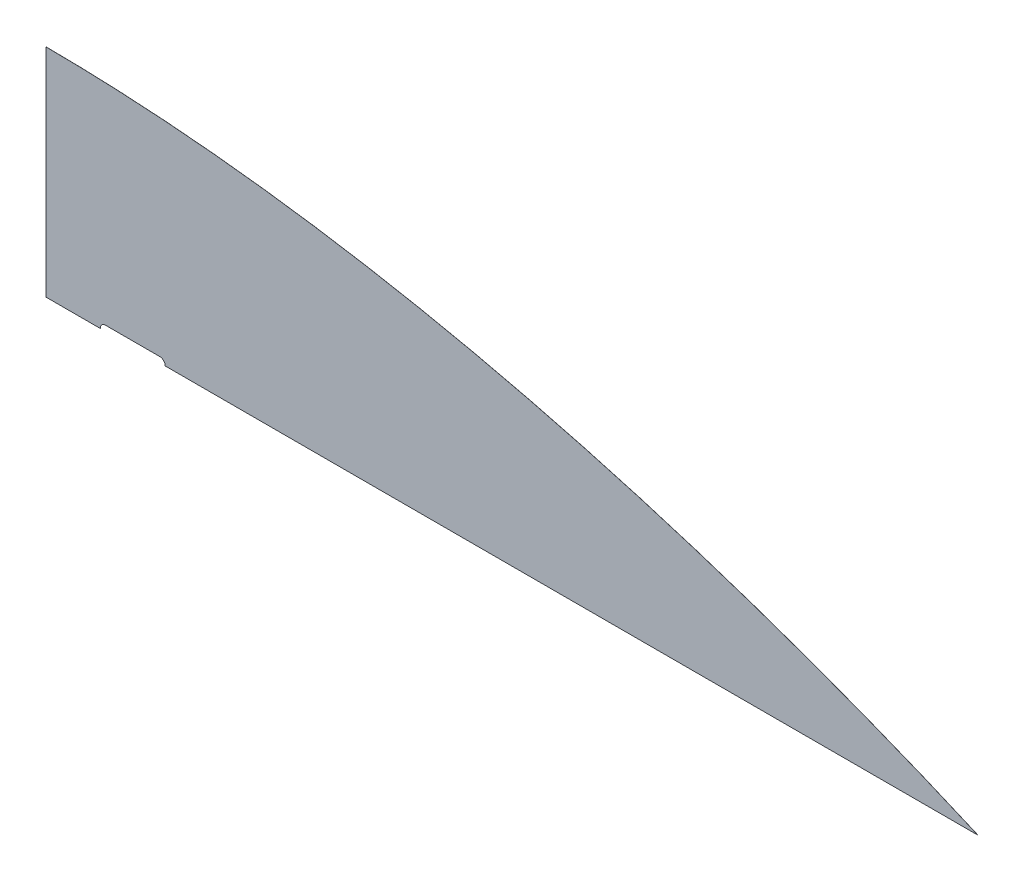
SolidWorks part; units mm, degrees
material "PC High Viscosity"
ref_plane "Front Plane" through (0, 0, 0) normal (0, 0, 1) x (1, 0, 0)
ref_plane "Top Plane" through (0, 0, 0) normal (0, 1, 0) x (1, 0, 0)
ref_plane "Right Plane" through (0, 0, 0) normal (1, 0, 0) x (0, 0, -1)
sketch "Sketch1" plane through (0, 0, 0) normal (0, 0, 1) x (1, 0, 0)
  line L0 (0, 254) -> (0, 0)
  line L1 (0, 0) -> (1092.2, 0)
  spline S0 degree 3 poles (0, 254) (376.5132, 252.2764) (770.2858, 140.4997) (1092.2, 0) knots 0 0 0 0 1 1 1 1
  dimension "D1" = 1092.2
  dimension "D2" = 254
extrude "Boss-Extrude1" add sketch "Sketch1" along normal blind 0.127
sketch "Sketch2" plane through (0, 0, 0.127) normal (0, 0, 1) x (1, 0, 0)
  line L0 (0, 30.48) -> (1020.0945, 30.48) construction
  line L1 (0, 254) -> (0, 0) construction
  line L2 (0, 0) -> (1092.2, 0) construction
  spline S0 degree 3 poles (1092.2, 0) (770.2858, 140.4997) (376.5132, 252.2764) (0, 254) knots 0 0 0 0 1 1 1 1 construction
  point P8 (63.5, 30.48)
  point P9 (977.9, 30.48)
  dimension "D1" = 30.48
  dimension "D2" = 63.5
  dimension "D3" = 914.4
hole_wizard "F (0.257) Diameter Hole1" [suppressed] positions "Sketch3" profile "Sketch4" hole size "F" standard "ANSI Inch"
sketch "Sketch3" plane through (0, 0, 6.35) normal (0, 0, 1) x (1, 0, 0)
  point P0 (63.5, 30.48)
  point P3 (977.9, 30.48)
sketch "Sketch4" plane through (63.5, 30.48, 6.35) normal (1, 0, 0) x (0, -1, 0)
  line L0 (0, 0) -> (0, 6.35)
  line L1 (0, 6.35) -> (3.2639, 6.35)
  line L2 (3.2639, 6.35) -> (3.2639, 0)
  line L5 (3.2639, 0) -> (0, 0)
  line L11 (0, -6.35) -> (0, 107.95) construction
  dimension "Thru Hole Dia." = 6.5278
  dimension "Thru Hole Depth" = 6.35
sketch "Sketch5" plane through (0, 0, 0) normal (0, 0, -1) x (-1, 0, 0)
  line L0 (0, 0) -> (-1092.2, 0) construction
  line L1 (-130.175, 0) -> (-247.65, 0)
  line L2 (-130.175, 0) -> (-130.175, -38.1)
  line L3 (-130.175, -38.1) -> (-247.65, -38.1)
  line L4 (-247.65, 0) -> (-247.65, -38.1)
  line L6 (-815.975, 0) -> (-933.45, 0)
  line L7 (-815.975, 0) -> (-815.975, -38.1)
  line L8 (-815.975, -38.1) -> (-933.45, -38.1)
  line L9 (-933.45, 0) -> (-933.45, -38.1)
  dimension "D1" = 130.175
  dimension "D2" = 568.325
  dimension "D3" = 117.475
  dimension "D4" = 38.1
extrude "Boss-Extrude2" [suppressed] add sketch "Sketch5" against normal up to surface (6.35 mm away)
fillet "Fillet1" [suppressed] radius 3.175
sketch "Sketch6" [suppressed] plane through (0, 0, 0) normal (0, 0, -1) x (-1, 0, 0)
  line L0 (-936.625, 0) -> (-127, 0) construction
  line L1 (-130.175, -6.35) -> (-933.45, -6.35) construction
  line L2 (-130.175, -34.925) -> (-130.175, -3.175) construction
  line L3 (-933.45, -3.175) -> (-933.45, -34.925) construction
  line L4 (-874.7125, -38.1) -> (-874.7125, 0) construction
  line L5 (-930.275, -38.1) -> (-819.15, -38.1) construction
  line L6 (-819.15, -38.1) -> (-244.475, -38.1) construction
  line L7 (-531.8125, -38.1) -> (-531.8125, 0) construction
  line L8 (-188.9125, -38.1) -> (-188.9125, 0) construction
  arc A0 (-933.45, -3.175) -> (-936.625, 0) centre (-936.625, -3.175) ccw construction
  circle A1 centre (-908.05, -9.7282) radius 3.3782
  circle A2 centre (-908.05, 3.3782) radius 3.3782
  circle A3 centre (-841.375, 3.3782) radius 3.3782
  circle A4 centre (-841.375, -9.7282) radius 3.3782
  circle A5 centre (-222.25, -9.7282) radius 3.3782
  circle A6 centre (-222.25, 3.3782) radius 3.3782
  circle A7 centre (-155.575, 3.3782) radius 3.3782
  circle A8 centre (-155.575, -9.7282) radius 3.3782
  dimension "D2" = 6.7564
  dimension "D1" = 6.35
  dimension "D3" = 25.4
extrude "Cut-Extrude1" [suppressed] cut sketch "Sketch6" against normal through all
sketch "Sketch7" plane through (0, 0, 0) normal (0, 0, -1) x (-1, 0, 0)
  line L0 (0, 0) -> (-1092.2, 0) construction
  line L1 (-63.5, 0) -> (-133.35, 0)
  line L3 (-69.85, 6.35) -> (-133.35, 6.35)
  line L4 (0, 0) -> (-1092.2, 0) construction
  arc A0 (-133.35, 6.35) -> (-139.7, 0) centre (-133.35, 0) ccw
  arc A1 (-69.85, 6.35) -> (-63.5, 0) centre (-69.85, 0) cw
  dimension "D1" = 6.35
  dimension "D2" = 63.5
  dimension "D3" = 63.5
extrude "Cut-Extrude2" cut sketch "Sketch7" against normal through all
sketch "Sketch8" plane through (0, 0, 0.127) normal (0, 0, 1) x (1, 0, 0)
  line L0 (139.7, 0) -> (1092.2, 0) construction
  line L1 (192.0875, 0) -> (890.5875, 0)
  line L2 (192.0875, 0) -> (192.0875, -57.15)
  line L3 (192.0875, -57.15) -> (890.5875, -57.15)
  line L4 (890.5875, 0) -> (890.5875, -57.15)
  dimension "D1" = 57.15
  dimension "D2" = 201.6125
  dimension "D3" = 52.3875
extrude "Boss-Extrude3" [suppressed] add sketch "Sketch8" against normal up to surface (0.127 mm away)
sketch "Sketch12" [suppressed] plane through (0, 0, 0.127) normal (0, 0, 1) x (1, 0, 0)
  line L0 (192.0875, -57.15) -> (890.5875, -57.15) construction
  line L1 (604.8375, -57.15) -> (546.1, -57.15)
  line L2 (604.8375, -57.15) -> (604.8375, 0)
  line L3 (604.8375, 0) -> (546.1, 0)
  line L4 (546.1, -57.15) -> (546.1, 0)
  line L5 (890.5875, -57.15) -> (890.5875, 0) construction
  line L6 (0, 254) -> (0, 0) construction
  line L7 (139.7, 0) -> (192.0875, 0) construction
  dimension "D1" = 285.75
  dimension "D2" = 546.1
extrude "Cut-Extrude3" [suppressed] cut sketch "Sketch12" against normal through all
fillet "Fillet2" [suppressed] radius 3.175
fillet "Fillet3" [suppressed] radius 6.35
sketch "Sketch9" [suppressed] plane through (0, 0, 0) normal (0, 0, -1) x (-1, 0, 0)
  line L4 (-192.0875, -50.8) -> (-192.0875, -3.175) construction
  line L5 (-884.2375, -57.15) -> (-611.1875, -57.15) construction
  line L6 (-890.5875, -3.175) -> (-890.5875, -50.8) construction
  point P0 (-234.95, -35.306)
  point P2 (-847.725, -35.306)
  dimension "D1" = 42.8625
  dimension "D2" = 21.844
  dimension "D3" = 42.8625
hole_wizard "F (0.257) Diameter Hole2" [suppressed] positions "Sketch10" profile "Sketch11" hole size "F" standard "ANSI Inch"
sketch "Sketch10" [suppressed] plane through (0, 0, 0) normal (0, 0, -1) x (-1, 0, 0)
  point P0 (-847.725, -35.306)
  point P3 (-234.95, -35.306)
sketch "Sketch11" plane through (847.725, -35.306, 0) normal (1, 0, 0) x (0, 1, 0)
  line L0 (0, 0) -> (0, 0.127)
  line L1 (0, 0.127) -> (3.2639, 0.127)
  line L2 (3.2639, 0.127) -> (3.2639, 0)
  line L5 (3.2639, 0) -> (0, 0)
  line L11 (0, -6.35) -> (0, 107.95) construction
  dimension "Thru Hole Dia." = 6.5278
  dimension "Thru Hole Depth" = 0.127
equation "\"D3@Sketch9\"=\"D1@Sketch9\""
